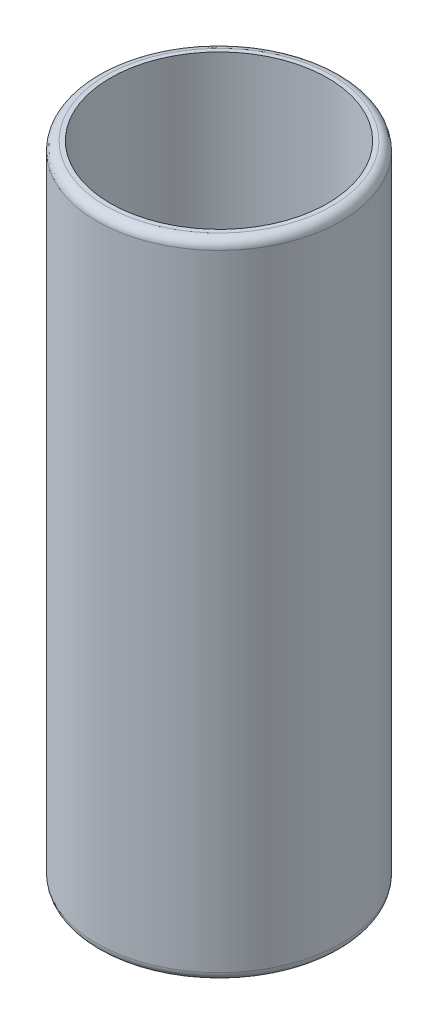
SolidWorks part; units mm, degrees
material "Glass"
ref_plane "Front Plane" through (0, 0, 0) normal (0, 0, 1) x (1, 0, 0)
ref_plane "Top Plane" through (0, 0, 0) normal (0, 1, 0) x (1, 0, 0)
ref_plane "Right Plane" through (0, 0, 0) normal (1, 0, 0) x (0, 0, -1)
sketch "Sketch1" plane through (0, 0, 0) normal (0, 1, 0) x (1, 0, 0)
  circle A0 centre (0, 0) radius 13.75
  dimension "D1" = 27.5
extrude "Boss-Extrude1" add sketch "Sketch1" along normal blind 72.5
sketch "Sketch2" plane through (0, 72.5, 0) normal (0, 1, 0) x (1, 0, 0)
  circle A0 centre (0, 0) radius 12.25
  circle A1 centre (0, 0) radius 13.75 construction
  dimension "D1" = 24.5
extrude "Cut-Extrude1" cut sketch "Sketch2" against normal blind 71
fillet "Fillet1" radius 1 2 edges at (0, 72.5, 13.75) (0, 0, 13.75)
